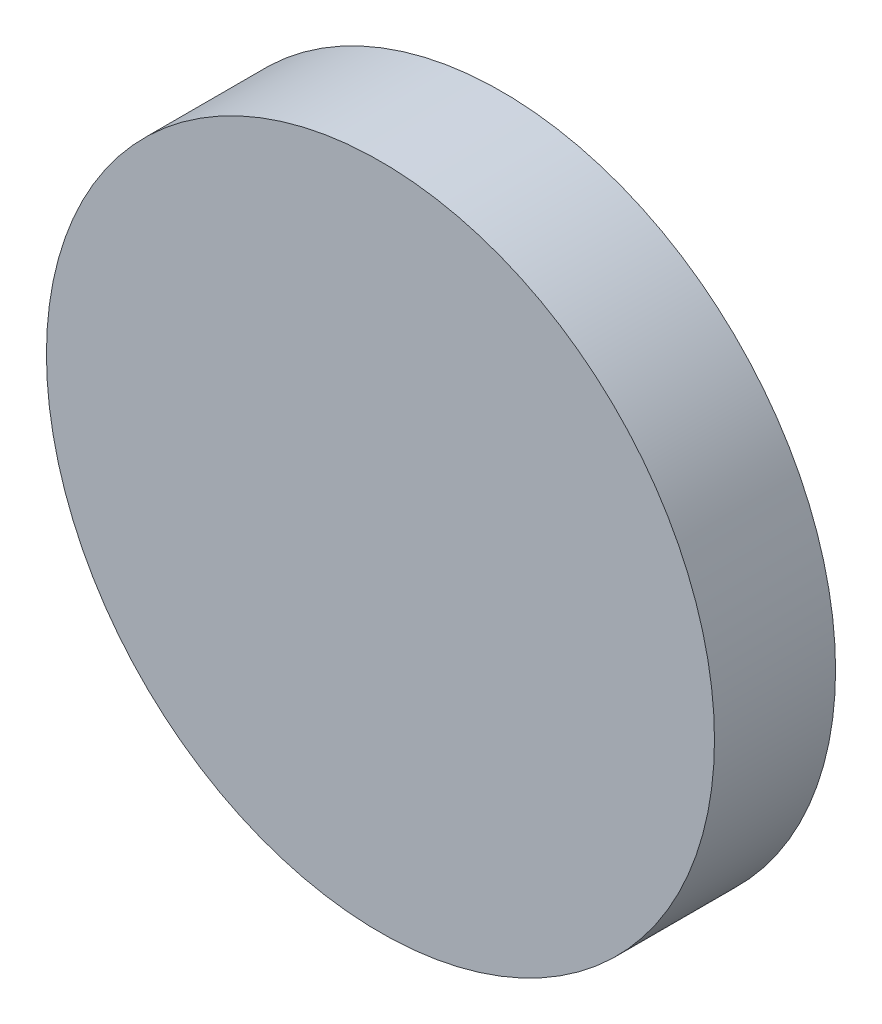
SolidWorks part; units mm, degrees
ref_plane "Front Plane" through (0, 0, 0) normal (0, 0, 1) x (1, 0, 0)
ref_plane "Top Plane" through (0, 0, 0) normal (0, 1, 0) x (1, 0, 0)
ref_plane "Right Plane" through (0, 0, 0) normal (1, 0, 0) x (0, 0, -1)
sketch "Sketch1" plane through (0, 0, 0) normal (0, 0, 1) x (1, 0, 0)
  circle A0 centre (-6.3954, 2.9287) radius 27.5858
extrude "Boss-Extrude1" add sketch "Sketch1" along normal blind 10
